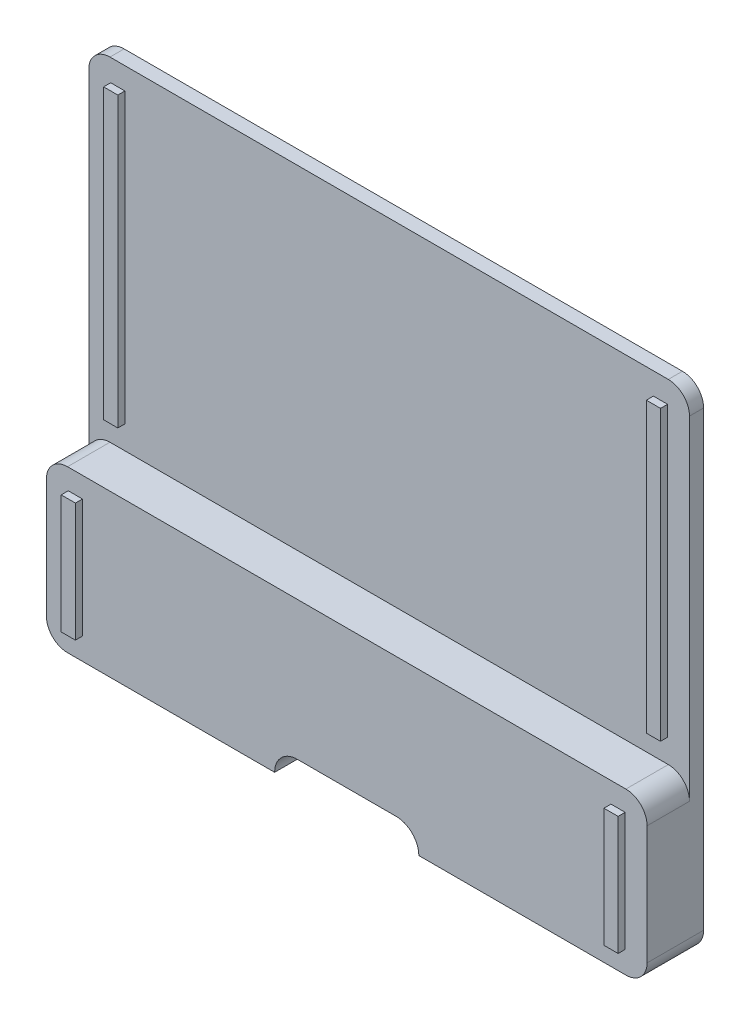
SolidWorks part; units mm, degrees
ref_plane "Front Plane" through (0, 0, 0) normal (0, 0, 1) x (1, 0, 0)
ref_plane "Top Plane" through (0, 0, 0) normal (0, 1, 0) x (1, 0, 0)
ref_plane "Right Plane" through (0, 0, 0) normal (1, 0, 0) x (0, 0, -1)
sketch "Sketch1" plane through (0, 0, 0) normal (0, 0, 1) x (1, 0, 0)
  line L0 (3, 70) -> (82, 70)
  line L8 (35.5, 3.2) -> (49.5, 3.2)
  line L9 (0, 67) -> (0, 3)
  line L10 (85, 67) -> (85, 3)
  line L15 (3, 0) -> (32.3, 0)
  line L17 (52.7, 0) -> (82, 0)
  arc A2 (82, 70) -> (85, 67) centre (82, 67) cw
  arc A3 (0, 67) -> (3, 70) centre (3, 67) cw
  arc A4 (35.5, 3.2) -> (32.3, 0) centre (35.5, 0) ccw
  arc A5 (52.7, 0) -> (49.5, 3.2) centre (49.5, 0) ccw
  arc A6 (82, 0) -> (85, 3) centre (82, 3) ccw
  arc A9 (0, 3) -> (3, 0) centre (3, 3) ccw
extrude "Boss-Extrude1" add sketch "Sketch1" along normal blind 8
sketch "Sketch2" plane through (0, 0, 8) normal (0, 0, 1) x (1, 0, 0)
  line L0 (3, 70) -> (82, 70)
  line L9 (3, 22.8) -> (82, 22.8)
  line L12 (0, 67) -> (0, 19.8)
  line L14 (85, 67) -> (85, 19.8)
  arc A2 (82, 70) -> (85, 67) centre (82, 67) cw
  arc A3 (0, 67) -> (3, 70) centre (3, 67) cw
  arc A6 (3, 22.8) -> (0, 19.8) centre (3, 19.8) ccw
  arc A7 (85, 19.8) -> (82, 22.8) centre (82, 19.8) ccw
extrude "Cut-Extrude1" cut sketch "Sketch2" against normal offset from surface (6 mm away) 2 up to face at (42.5, 23.9771, 0)
sketch "Sketch3" plane through (0, 0, 8) normal (0, 0, 1) x (1, 0, 0)
  line L9 (3.1, 3.1) -> (5.11, 3.1)
  line L10 (3.1, 3.1) -> (3.1, 19.9)
  line L11 (3.1, 19.9) -> (5.11, 19.9)
  line L12 (5.11, 3.1) -> (5.11, 19.9)
  line L13 (81.9, 3.1) -> (79.89, 3.1)
  line L14 (81.9, 3.1) -> (81.9, 19.9)
  line L15 (81.9, 19.9) -> (79.89, 19.9)
  line L16 (79.89, 3.1) -> (79.89, 19.9)
extrude "Boss-Extrude2" add sketch "Sketch3" along normal blind 1
sketch "Sketch4" plane through (0, 0, 2) normal (0, 0, 1) x (1, 0, 0)
  line L9 (3.1, 66.9) -> (5.11, 66.9)
  line L10 (3.1, 66.9) -> (3.1, 26.1)
  line L11 (3.1, 26.1) -> (5.11, 26.1)
  line L12 (5.11, 66.9) -> (5.11, 26.1)
  line L13 (81.9, 66.9) -> (79.89, 66.9)
  line L14 (81.9, 66.9) -> (81.9, 26.1)
  line L15 (81.9, 26.1) -> (79.89, 26.1)
  line L16 (79.89, 66.9) -> (79.89, 26.1)
extrude "Boss-Extrude3" add sketch "Sketch4" along normal blind 1
